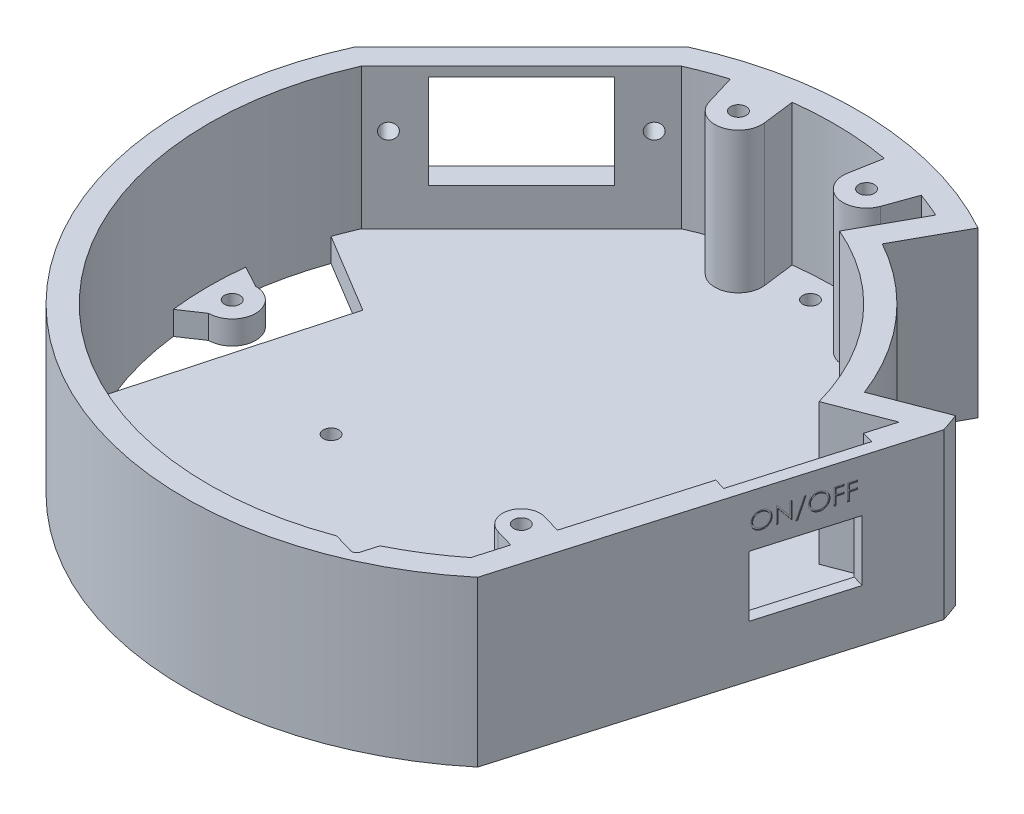
SolidWorks part; units mm, degrees
ref_plane "Front Plane" through (0, 0, 0) normal (0, 0, 1) x (1, 0, 0)
ref_plane "Top Plane" through (0, 0, 0) normal (0, 1, 0) x (1, 0, 0)
ref_plane "Right Plane" through (0, 0, 0) normal (1, 0, 0) x (0, 0, -1)
sketch "Sketch1" plane through (0, 0, 0) normal (0, 1, 0) x (1, 0, 0)
  line L0 (45.7364, -55.017) -> (68.1495, 21.7792)
  line L1 (0, 0) -> (0, 115.6527) construction
  line L2 (0, 0) -> (50000, 0) construction
  line L3 (34.5874, 62.6291) -> (27.3358, 49.4984)
  line L4 (66.793, 25.6394) -> (52.7893, 20.2639)
  line L5 (27.3358, 49.4984) -> (0, 0) construction
  line L6 (0, 0) -> (52.7893, 20.2639) construction
  line L7 (-65.0786, 29.7232) -> (-29.7232, 65.0786)
  line L8 (-47.4009, 47.4009) -> (0, 0) construction
  arc A0 (68.1495, 21.7792) -> (66.793, 25.6394) centre (0, 0) ccw
  arc A1 (27.3358, 49.4984) -> (52.7893, 20.2639) centre (0, 0) cw
  arc A2 (34.5874, 62.6291) -> (-29.7232, 65.0786) centre (0, 0) ccw
  arc A3 (-65.0786, 29.7232) -> (45.7364, -55.017) centre (0, 0) ccw
  dimension "D1" = 143.09
  dimension "D2" = 80
  dimension "D3" = 16.27
  dimension "D4" = 15
  dimension "D5" = 21
  dimension "D6" = 40.09
  dimension "D7" = 45
  dimension "D8" = 50
extrude "Boss-Extrude1" add sketch "Sketch1" along normal blind 5
sketch "Sketch2" plane through (0, 5, 0) normal (0, 1, 0) x (1, 0, 0)
  line L0 (0, 0) -> (50.59, 50.59) construction
  line L1 (0, 0) -> (3.7444, -71.447) construction
  line L2 (0, 0) -> (-50.59, -50.59) construction
  line L3 (0, 0) -> (-71.545, 0) construction
  line L5 (0, 0) -> (0, -71.545) construction
  line L6 (0, 0) -> (0, 71.545) construction
  arc A1 (68.1495, 21.7792) -> (66.793, 25.6394) centre (0, 0) ccw construction
  circle A2 centre (0, 61.55) radius 1.65
  circle A3 centre (-43.5224, -43.5224) radius 1.65
  circle A4 centre (-61.55, 0) radius 1.65
  circle A6 centre (3.2213, -61.4656) radius 1.65
  point P20 (0, 0)
  dimension "D1" = 3.3
  dimension "D2" = 61.55
  dimension "D4" = 3.3
  dimension "D6" = 61.55
  dimension "D5" = 3
  dimension "D3" = 61.55
extrude "Cut-Extrude1" cut sketch "Sketch2" against normal through all
sketch "Sketch3" plane through (0, 5, 0) normal (0, 1, 0) x (1, 0, 0)
  line L0 (34.5874, 62.6291) -> (27.3358, 49.4984)
  line L2 (41.3733, -52.1199) -> (61.9634, 18.4298)
  line L3 (41.3733, -52.1199) -> (61.9634, 18.4298)
  line L4 (52.7893, 20.2639) -> (66.793, 25.6394)
  line L5 (45.7364, -55.017) -> (68.1495, 21.7792)
  line L6 (45.7364, -55.017) -> (68.1495, 21.7792)
  line L7 (61.9634, 18.4298) -> (49.6863, 13.7171)
  line L8 (61.9634, 18.4298) -> (49.6863, 13.7171)
  line L9 (20.4243, 47.3259) -> (27.7024, 60.5047)
  line L10 (20.4243, 47.3259) -> (27.7024, 60.5047)
  line L11 (-29.7232, 65.0786) -> (-65.0786, 29.7232)
  line L12 (-60.8933, 26.8374) -> (-26.8374, 60.8933)
  line L13 (0, 0) -> (-47.4009, 47.4009)
  line L14 (0, 0) -> (0, 50000) construction
  line L19 (-26.8374, 60.8933) -> (-60.8933, 26.8374)
  line L20 (-26.8374, 60.8933) -> (-60.8933, 26.8374)
  arc A0 (34.5874, 62.6291) -> (-29.7232, 65.0786) centre (0, 0) ccw
  arc A1 (34.5874, 62.6291) -> (-29.7232, 65.0786) centre (0, 0) ccw construction
  arc A2 (27.7024, 60.5047) -> (-26.8374, 60.8933) centre (0, 0) ccw
  arc A4 (27.3358, 49.4984) -> (52.7893, 20.2639) centre (0, 0) cw
  arc A5 (27.7024, 60.5047) -> (-26.8374, 60.8933) centre (0, 0) ccw
  arc A6 (68.1495, 21.7792) -> (66.793, 25.6394) centre (0, 0) ccw
  arc A7 (68.1495, 21.7792) -> (66.793, 25.6394) centre (0, 0) ccw
  arc A8 (49.6863, 13.7171) -> (20.4243, 47.3259) centre (0, 0) ccw
  arc A9 (49.6863, 13.7171) -> (20.4243, 47.3259) centre (0, 0) ccw
  arc A10 (52.7893, 20.2639) -> (27.3358, 49.4984) centre (0, 0) ccw construction
  arc A11 (-65.0786, 29.7232) -> (45.7364, -55.017) centre (0, 0) ccw
  arc A12 (-60.8933, 26.8374) -> (41.3733, -52.1199) centre (0, 0) ccw
  arc A17 (-60.8933, 26.8374) -> (41.3733, -52.1199) centre (0, 0) ccw
  arc A18 (-60.8933, 26.8374) -> (41.3733, -52.1199) centre (0, 0) ccw
  point P26 (-43.8653, 43.8653)
  arc M9 (68.1495, 21.7792) -> (66.793, 25.6394) centre (0, 0) ccw
  line M10 (45.7364, -55.017) -> (68.1495, 21.7792)
  arc M11 (34.5874, 62.6291) -> (-29.7232, 65.0786) centre (0, 0) ccw
  line M12 (66.793, 25.6394) -> (52.7893, 20.2639)
  arc M13 (52.7893, 20.2639) -> (27.3358, 49.4984) centre (0, 0) ccw
  line M14 (27.3358, 49.4984) -> (34.5874, 62.6291)
  line M29 (-29.7232, 65.0786) -> (-65.0786, 29.7232)
  arc M30 (-65.0786, 29.7232) -> (45.7364, -55.017) centre (0, 0) ccw
  dimension "D3" = 5
  dimension "D4" = 50
  dimension "D5" = 45
  dimension "D1" = 5
  dimension "D2" = 0
extrude "Boss-Extrude3" add sketch "Sketch3" along normal blind 30 contours L14 A12 L12 L13 L11 M30 | A5 L14 A0 L13 L12 M29 | L14 A11 A5 L10 A9 L8 L3 A18 M10 M9 M12 M13 M14 M11
ref_plane "Plane1" through (42.5437, 0, 12.4165) normal (-0.96, 0, -0.2802) x (-0.2802, 0, 0.96)
ref_plane "Plane2" through (-10.7699, 0, 36.9018) normal (0.2802, 0, -0.96) x (0, -1, 0)
sketch "Sketch4" plane through (-10.7699, 0, 36.9018) normal (0.2802, 0, -0.96) x (0, -1, 0)
  line L0 (-19, -41.5685) -> (-35, -41.5685) construction
  line L1 (-19, -45.0685) -> (-35, -45.0685)
  line L2 (-19, -38.0685) -> (-35, -38.0685)
  line L3 (16.5, -44.3185) -> (-16.5, -44.3185) construction
  arc A0 (-19, -45.0685) -> (-19, -38.0685) centre (-19, -41.5685) ccw
  arc A1 (-35, -38.0685) -> (-35, -45.0685) centre (-35, -41.5685) ccw
  point P2 (-27, -41.5685)
  dimension "D1" = 3.5
  dimension "D2" = 14
  dimension "D4" = 2.75
extrude "Cut-Extrude2" cut sketch "Sketch4" against normal blind 15
fillet "Fillet1" radius 1 2 edges at (26.5293, 15.9211, 63.4135) (28.2913, 27, 63.9277)
sketch "Sketch5" plane through (0, 5, 0) normal (0, 1, 0) x (1, 0, 0)
  line L1 (47.1664, 3.4228) -> (37.921, -28.2557) construction
  line L3 (5.0693, -41.5245) -> (-26.6091, -32.2791) construction
  circle A0 centre (26.5691, -29.6734) radius 1.65
  circle A1 centre (-26.2282, -14.2644) radius 1.65
  dimension "D1" = 17.4
  dimension "D2" = 3.3
  dimension "D4" = 3.3
  dimension "D5" = 10.5
  dimension "D6" = 65.5
  dimension "D3" = 17.4
extrude "Cut-Extrude3" cut sketch "Sketch5" against normal through all
ref_plane "Plane3" through (0, 0, 0) normal (0.7071, 0, 0.7071) x (0.7071, 0, -0.7071)
sketch "Sketch6" plane through (0, 0, 0) normal (0.7071, 0, 0.7071) x (0.7071, 0, -0.7071)
  line L2 (14, 33) -> (14, 13)
  line L3 (14, 13) -> (-14, 13)
  line L4 (-14, 33) -> (-14, 13)
  line L5 (14, 33) -> (-14, 33)
  line L7 (20, 23) -> (14, 23) construction
  line L8 (-14, 23) -> (-20, 23) construction
  line L9 (-6.5624, 35) -> (63.5892, 35) construction
  circle A0 centre (20, 23) radius 1.65
  circle A1 centre (-20, 23) radius 1.65
  point P8 (-14, 23)
  point P9 (14, 23)
  point P10 (0, 13)
  dimension "D1" = 3.3
  dimension "D5" = 40
  dimension "D2" = 28
  dimension "D3" = 20
  dimension "D4" = 2
extrude "Cut-Extrude4" cut sketch "Sketch6" against normal through all
sketch "Sketch7" plane through (56.9429, 0, 16.6189) normal (0.96, 0, 0.2802) x (0.2802, 0, -0.96)
  line L0 (-40, 0) -> (40, 0) construction
  line L1 (6.6, 11.05) -> (26, 11.05)
  line L2 (6.6, 11.05) -> (6.6, 23.95)
  line L3 (6.6, 23.95) -> (26, 23.95)
  line L4 (26, 11.05) -> (26, 23.95)
  line L6 (40, 35) -> (40, 0) construction
  point P8 (26, 17.5)
  dimension "D1" = 19.4
  dimension "D2" = 12.9
  dimension "D3" = 17.5
  dimension "D4" = 14
extrude "Cut-Extrude5" cut sketch "Sketch7" against normal blind 5
sketch "Sketch8" plane through (56.9429, 0, 16.6189) normal (0.96, 0, 0.2802) x (0.2802, 0, -0.96)
  line L1 (3.6, 5) -> (29, 5)
  line L2 (3.6, 5) -> (3.6, 35)
  line L3 (3.6, 35) -> (29, 35)
  line L4 (29, 5) -> (29, 35)
  line L5 (-40, 35) -> (40, 35) construction
  line L6 (26, 11.05) -> (26, 23.95) construction
  line L7 (6.6, 23.95) -> (6.6, 11.05) construction
  line L8 (-40, 0) -> (40, 0) construction
  dimension "D1" = 3
  dimension "D2" = 3
  dimension "D3" = 5
extrude "Cut-Extrude6" cut sketch "Sketch8" against normal blind 5 from offset 2.5 offset against normal yes
sketch "Sketch9" plane through (56.9429, 0, 16.6189) normal (0.96, 0, 0.2802) x (0.2802, 0, -0.96)
  text T0 "ON/OFF"
extrude "Cut-Extrude7" cut sketch "Sketch9" against normal blind 0.2
sketch "Sketch10" plane through (0, 0, 0) normal (0, 1, 0) x (1, 0, 0)
  line L0 (-61.55, -5) -> (-66.0593, -8.0251)
  line L1 (-61.55, 5) -> (-66.1233, 7.4797)
  line L2 (-57.9606, -32.6926) -> (-45.7443, 12.0012)
  line L3 (-45.7443, 12.0012) -> (-62.7264, 22.2179)
  arc A0 (-61.55, -5) -> (-61.55, 5) centre (-61.55, 0) ccw
  arc A1 (-60.8933, 26.8374) -> (23.0915, -62.4101) centre (0, 0) ccw construction
  arc A2 (-66.1233, 7.4797) -> (-62.7264, 22.2179) centre (0, 0) cw
  arc A3 (-66.0593, -8.0251) -> (-57.9606, -32.6926) centre (0, 0) ccw
  arc A4 (-60.8933, 26.8374) -> (41.3733, -52.1199) centre (0, 0) ccw construction
  dimension "D1" = 10
extrude "Cut-Extrude8" cut sketch "Sketch10" along normal blind 6
sketch "Sketch11" plane through (0, 0, 0) normal (0, 1, 0) x (1, 0, 0)
  line L0 (20.2341, 56.2635) -> (22.5197, 62.6187)
  line L1 (10.6085, 58.8427) -> (11.8067, 65.4892)
  line L2 (10.6085, 58.8427) -> (0, 0) construction
  line L3 (0, 0) -> (20.2341, 56.2635) construction
  line L4 (41.6963, -36.7358) -> (45.5361, -37.8565)
  line L5 (15.5291, 57.9555) -> (0, 0) construction
  line L6 (0, 0) -> (50000, 0) construction
  line L7 (-17.2618, 57.2454) -> (-19.2116, 63.7115)
  line L8 (-7.5143, 59.3172) -> (-8.3631, 66.0174)
  line L9 (-17.2618, 57.2454) -> (0, 0) construction
  line L10 (0, 0) -> (-7.5143, 59.3172) construction
  line L11 (-12.4747, 58.6889) -> (0, 0) construction
  line L12 (41.3733, -52.1199) -> (53.1518, -11.7623) construction
  line L13 (39.455, -44.4155) -> (43.2948, -45.5361)
  line L14 (41.3733, -52.1199) -> (53.1518, -11.7623) construction
  line L15 (0, 0) -> (40.5756, -40.5756) construction
  line L16 (45.5361, -37.8565) -> (43.2948, -45.5361)
  circle A0 centre (15.5291, 57.9555) radius 1.65
  arc A1 (10.6085, 58.8427) -> (20.2341, 56.2635) centre (15.5291, 57.9555) ccw
  arc A2 (27.7024, 60.5047) -> (-26.8374, 60.8933) centre (0, 0) ccw construction
  arc A3 (11.8067, 65.4892) -> (22.5197, 62.6187) centre (0, 0) cw
  circle A4 centre (-12.4747, 58.6889) radius 1.65
  arc A5 (-17.2618, 57.2454) -> (-7.5143, 59.3172) centre (-12.4747, 58.6889) ccw
  arc A6 (27.7024, 60.5047) -> (-26.8374, 60.8933) centre (0, 0) ccw construction
  arc A7 (-19.2116, 63.7115) -> (-8.3631, 66.0174) centre (0, 0) cw
  circle A8 centre (40.5756, -40.5756) radius 1.65
  arc A9 (41.6963, -36.7358) -> (39.455, -44.4155) centre (40.5756, -40.5756) ccw
  dimension "D1" = 105
  dimension "D2" = 3.3
  dimension "D3" = 10
  dimension "D6" = 3.3
  dimension "D7" = 8
  dimension "D4" = 60
  dimension "D5" = 78
  dimension "D8" = 4
  dimension "D9" = 45
extrude "Boss-Extrude4" add sketch "Sketch11" along normal blind 35 contours A3 L1 A1 L0 A0 | L8 A7 L7 A5 | L16 L13 A9 L4 | A8 | A4
sketch "Sketch12" plane through (0, 35, 0) normal (0, 1, 0) x (1, 0, 0)
  line L1 (18.7046, 57.9555) -> (17.1169, 60.7055)
  line L2 (17.1169, 60.7055) -> (13.9414, 60.7055)
  line L3 (13.9414, 60.7055) -> (12.3537, 57.9555)
  line L4 (12.3537, 57.9555) -> (13.9414, 55.2055)
  line L5 (13.9414, 55.2055) -> (17.1169, 55.2055)
  line L6 (17.1169, 55.2055) -> (18.7046, 57.9555)
  line L7 (-9.2993, 58.6889) -> (-10.887, 61.4389)
  line L8 (-10.887, 61.4389) -> (-14.0624, 61.4389)
  line L9 (-14.0624, 61.4389) -> (-15.6501, 58.6889)
  line L10 (-15.6501, 58.6889) -> (-14.0624, 55.9389)
  line L11 (-14.0624, 55.9389) -> (-10.887, 55.9389)
  line L12 (-10.887, 55.9389) -> (-9.2993, 58.6889)
  line L13 (43.7511, -40.5756) -> (42.1634, -37.8256)
  line L14 (42.1634, -37.8256) -> (38.9879, -37.8256)
  line L15 (38.9879, -37.8256) -> (37.4002, -40.5756)
  line L16 (37.4002, -40.5756) -> (38.9879, -43.3256)
  line L17 (38.9879, -43.3256) -> (42.1634, -43.3256)
  line L18 (42.1634, -43.3256) -> (43.7511, -40.5756)
  circle A0 centre (15.5291, 57.9555) radius 2.75 construction
  circle A1 centre (-12.4747, 58.6889) radius 2.75 construction
  circle A2 centre (40.5756, -40.5756) radius 2.75 construction
  dimension "D1" = 5.5
extrude "Cut-Extrude9" cut sketch "Sketch12" against normal blind 2.6 from offset 3
